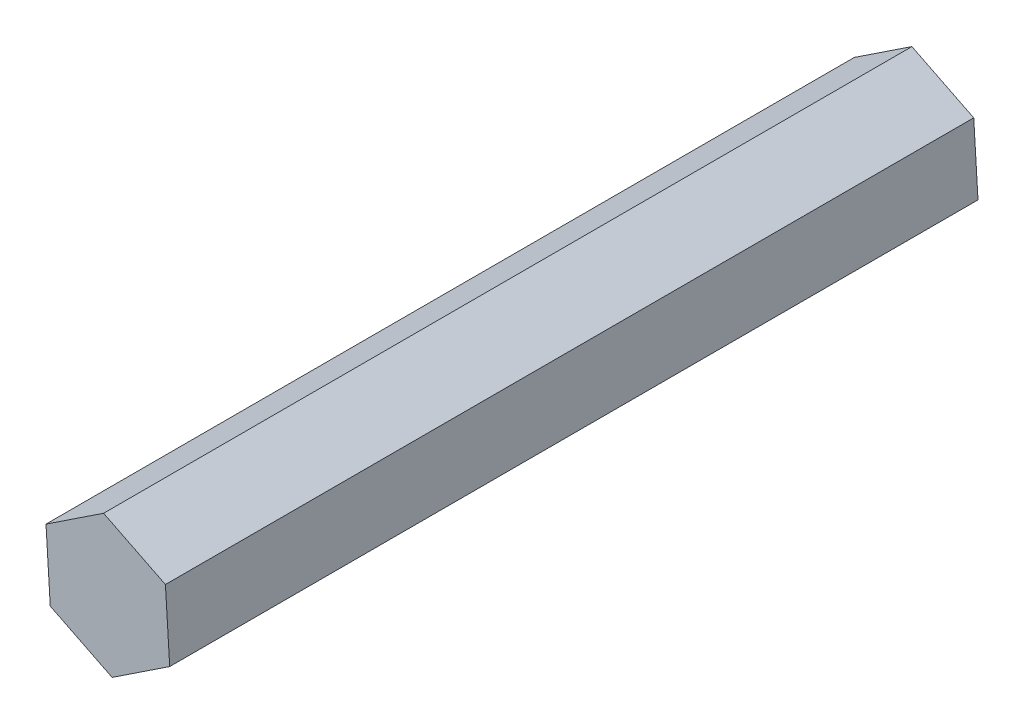
SolidWorks part; units mm, degrees
ref_plane "Front Plane" through (0, 0, 0) normal (0, 0, 1) x (1, 0, 0)
ref_plane "Top Plane" through (0, 0, 0) normal (0, 1, 0) x (1, 0, 0)
ref_plane "Right Plane" through (0, 0, 0) normal (1, 0, 0) x (0, 0, -1)
sketch "Sketch1" plane through (0, 0, 0) normal (0, 0, 1) x (1, 0, 0)
  line L1 (-0.4538, 7.336) -> (-6.58, 3.275)
  line L2 (-6.58, 3.275) -> (-6.1263, -4.061)
  line L3 (-6.1263, -4.061) -> (0.4538, -7.336)
  line L4 (0.4538, -7.336) -> (6.58, -3.275)
  line L5 (6.58, -3.275) -> (6.1263, 4.061)
  line L6 (6.1263, 4.061) -> (-0.4538, 7.336)
  circle A0 centre (0, 0) radius 6.3653 construction
  dimension "D1" = 7.35
extrude "Boss-Extrude1" add sketch "Sketch1" along normal blind 86
